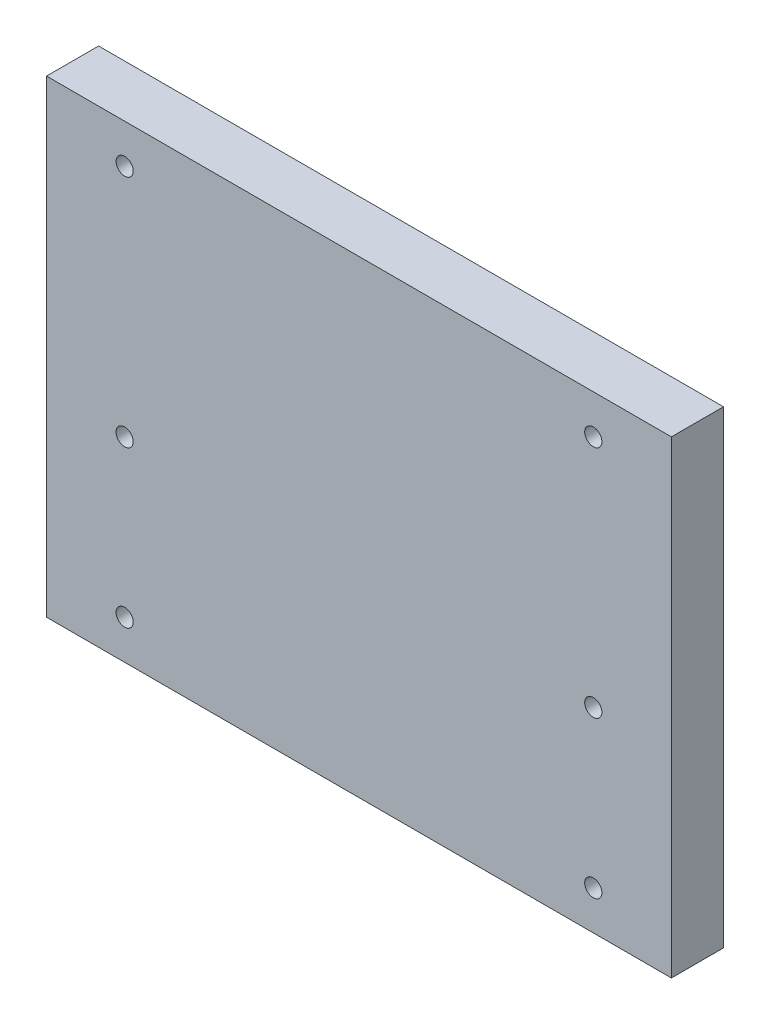
SolidWorks part; units mm, degrees
material "1023 Листовая углеродистая сталь (SS)"
ref_plane "Front" through (0, 0, 0) normal (0, 0, 1) x (1, 0, 0)
ref_plane "Top" through (0, 0, 0) normal (0, 1, 0) x (1, 0, 0)
ref_plane "Right" through (0, 0, 0) normal (1, 0, 0) x (0, 0, -1)
sketch "Sketch1" plane through (0, 0, 0) normal (0, 0, 1) x (1, 0, 0)
  line L1 (-120, 90) -> (120, 90)
  line L2 (-120, 90) -> (-120, -90)
  line L3 (-120, -90) -> (120, -90)
  line L4 (120, 90) -> (120, -90)
  line L5 (-120, 90) -> (120, -90) construction
  line L6 (-120, -90) -> (120, 90) construction
  point P0 (0, 0)
  dimension "D1" = 180
  dimension "D2" = 240
extrude "Extrude1" add sketch "Sketch1" along normal blind 20
hole_wizard "CBORE for M6 Hex Socket Head Cap Screw1" positions "Sketch4" profile "Sketch3" counterbore size "M6" standard "DIN" end condition through all
sketch "Sketch4" plane through (0, 0, 0) normal (0, 0, -1) x (-1, 0, 0)
  line L0 (-120, -90) -> (-120, 90) construction
  line L1 (120, -90) -> (-120, -90) construction
  line L2 (-120, 90) -> (120, 90) construction
  line L3 (0, 0) -> (0, 47.0775) construction
  point P0 (-90, 75)
  point P2 (-90, -75)
  point P4 (-90, -15)
  point P19 (90, -15)
  point P20 (90, -75)
  point P21 (90, 75)
  dimension "D1" = 30
  dimension "D2" = 15
  dimension "D3" = 15
  dimension "D4" = 105
sketch "Sketch3" plane through (90, 75, 0) normal (1, 0, 0) x (0, 1, 0)
  line L0 (0, 0) -> (0, 20)
  line L1 (0, 20) -> (3.3, 20)
  line L3 (3.3, 20) -> (3.3, 6.4)
  line L4 (3.3, 6.4) -> (5.5, 6.4)
  line L5 (5.5, 6.4) -> (5.5, 0)
  line L7 (5.5, 0) -> (0, 0)
  line L11 (0, -6.35) -> (0, 107.95) construction
  dimension "Диаметр сквозного отверстия" = 6.6
  dimension "Глубина сквозного отверстия" = 20
  dimension "Диаметр цековки" = 11
  dimension "Глубина цековки" = 6.4
